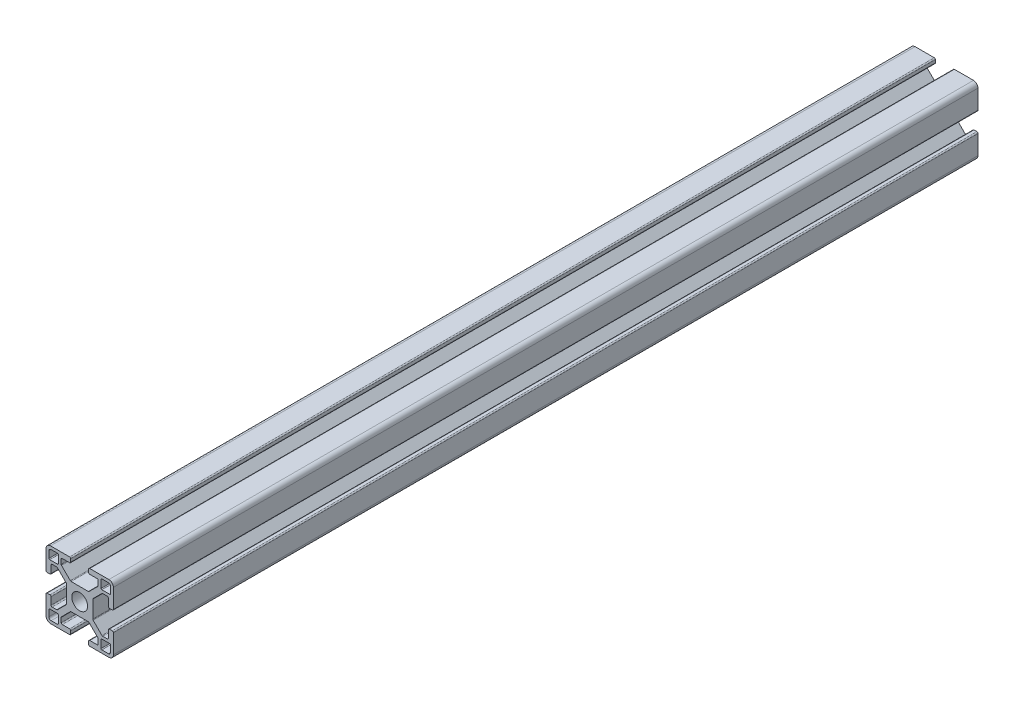
SolidWorks part; units mm, degrees
ref_plane "Front Plane" through (0, 0, 0) normal (0, 0, 1) x (1, 0, 0)
ref_plane "Top Plane" through (0, 0, 0) normal (0, 1, 0) x (1, 0, 0)
ref_plane "Right Plane" through (0, 0, 0) normal (1, 0, 0) x (0, 0, -1)
sketch "Sketch1" plane through (0, 0, 0) normal (0, 0, 1) x (1, 0, 0)
  line L0 (3.9799, -2.4733) -> (3.1981, -1.4942) construction
  line L1 (1.4942, -3.1981) -> (2.4733, -3.9799) construction
  line L2 (-2.4733, -3.9799) -> (-1.4942, -3.1981) construction
  line L3 (-3.1981, -1.4942) -> (-3.9799, -2.4733) construction
  line L4 (-3.9799, 2.4733) -> (-3.1981, 1.4942) construction
  line L5 (-1.4942, 3.1981) -> (-2.4733, 3.9799) construction
  line L6 (2.4733, 3.9799) -> (1.4942, 3.1981) construction
  line L7 (3.1981, 1.4942) -> (3.9799, 2.4733) construction
  line L8 (-12.6999, -13.6999) -> (-9.881, -13.6999)
  line L9 (-13.6999, -9.881) -> (-13.6999, -12.6999)
  line L10 (-9.88, -9.5) -> (-13.3189, -9.5)
  line L11 (-9.5, -13.3189) -> (-9.5, -9.88)
  line L12 (13.6999, -12.6999) -> (13.6999, -9.881)
  line L13 (9.881, -13.6999) -> (12.6999, -13.6999)
  line L14 (9.5, -9.88) -> (9.5, -13.3189)
  line L15 (13.3189, -9.5) -> (9.88, -9.5)
  line L16 (9.88, 9.5) -> (13.3189, 9.5)
  line L17 (9.5, 13.3189) -> (9.5, 9.88)
  line L18 (12.6999, 13.6999) -> (9.881, 13.6999)
  line L19 (13.6999, 9.881) -> (13.6999, 12.6999)
  line L20 (-13.6999, 12.6999) -> (-13.6999, 9.881)
  line L21 (-9.881, 13.6999) -> (-12.6999, 13.6999)
  line L22 (-9.5, 9.88) -> (-9.5, 13.3189)
  line L23 (-13.3189, 9.5) -> (-9.88, 9.5)
  line L24 (14.4999, -4) -> (13.2425, -4)
  line L25 (12.7425, -4.5) -> (12.7425, -7.7325)
  line L26 (12.2428, -8.25) -> (10.2602, -8.25)
  line L27 (9.9066, -8.1035) -> (5.9811, -4.178)
  line L28 (5.8347, -3.8245) -> (5.8347, -1.0125)
  line L29 (5.8347, -1.0125) -> (5.3247, -0.0625) construction
  line L30 (5.3247, -0.0625) -> (5.8347, 0.8875) construction
  line L31 (5.8347, 0.8875) -> (5.8347, 3.8245)
  line L32 (5.9811, 4.178) -> (9.9066, 8.1035)
  line L33 (10.2602, 8.25) -> (12.2428, 8.25)
  line L34 (12.7425, 7.7325) -> (12.7425, 4.5)
  line L35 (13.2425, 4) -> (14.4999, 4)
  line L36 (14.9999, 4.5) -> (14.9999, 12.9999)
  line L37 (12.9999, 14.9999) -> (4.5, 14.9999)
  line L38 (4, 14.4999) -> (4, 13.2425)
  line L39 (4.5, 12.7425) -> (7.7325, 12.7425)
  line L40 (8.25, 12.2428) -> (8.25, 10.2602)
  line L41 (8.1035, 9.9066) -> (4.178, 5.9811)
  line L42 (3.8245, 5.8347) -> (0.95, 5.8347)
  line L43 (0.95, 5.8347) -> (0, 5.3247) construction
  line L44 (0, 5.3247) -> (-0.95, 5.8347) construction
  line L45 (-0.95, 5.8347) -> (-3.8245, 5.8347)
  line L46 (-4.178, 5.9811) -> (-8.1035, 9.9066)
  line L47 (-8.25, 10.2602) -> (-8.25, 12.2428)
  line L48 (-7.7325, 12.7425) -> (-4.5, 12.7425)
  line L49 (-4, 13.2425) -> (-4, 14.4999)
  line L50 (-4.5, 14.9999) -> (-12.9999, 14.9999)
  line L51 (-14.9999, 12.9999) -> (-14.9999, 4.5)
  line L52 (-14.4999, 4) -> (-13.2425, 4)
  line L53 (-12.7425, 4.5) -> (-12.7425, 7.7325)
  line L54 (-12.2428, 8.25) -> (-10.2602, 8.25)
  line L55 (-9.9066, 8.1035) -> (-5.9811, 4.178)
  line L56 (-5.8347, 3.8245) -> (-5.8347, 0.8875)
  line L57 (-5.8347, 0.8875) -> (-5.3247, -0.0625) construction
  line L58 (-5.3247, -0.0625) -> (-5.8347, -1.0125) construction
  line L59 (-5.8347, -1.0125) -> (-5.8347, -3.8245)
  line L60 (-5.9811, -4.178) -> (-9.9066, -8.1035)
  line L61 (-10.2602, -8.25) -> (-12.2428, -8.25)
  line L62 (-12.7425, -7.7325) -> (-12.7425, -4.5)
  line L63 (-13.2425, -4) -> (-14.4999, -4)
  line L64 (-14.9999, -4.5) -> (-14.9999, -12.9999)
  line L65 (-12.9999, -14.9999) -> (-4.5, -14.9999)
  line L66 (-4, -14.4999) -> (-4, -13.2425)
  line L67 (-4.5, -12.7425) -> (-7.7325, -12.7425)
  line L68 (-8.25, -12.2428) -> (-8.25, -10.2602)
  line L69 (-8.1035, -9.9066) -> (-4.178, -5.9811)
  line L70 (-3.8245, -5.8347) -> (-0.95, -5.8347)
  line L71 (-0.95, -5.8347) -> (0, -5.3247) construction
  line L72 (0, -5.3247) -> (0.95, -5.8347) construction
  line L73 (0.95, -5.8347) -> (3.8245, -5.8347)
  line L74 (4.178, -5.9811) -> (8.1035, -9.9066)
  line L75 (8.25, -10.2602) -> (8.25, -12.2428)
  line L76 (7.7325, -12.7425) -> (4.5, -12.7425)
  line L77 (4, -13.2425) -> (4, -14.4999)
  line L78 (4.5, -14.9999) -> (12.9999, -14.9999)
  line L79 (14.9999, -12.9999) -> (14.9999, -4.5)
  line L80 (-5.8347, -1.0125) -> (-5.8347, 0.8875)
  line L81 (-0.95, 5.8347) -> (0.95, 5.8347)
  line L82 (5.8347, 0.8875) -> (5.8347, -1.0125)
  line L83 (-0.95, -5.8347) -> (0.95, -5.8347)
  arc A0 (2.4733, -3.9799) -> (3.9799, -2.4733) centre (3.1422, -3.1422) ccw construction
  arc A1 (-1.4942, -3.1981) -> (1.4942, -3.1981) centre (0, 0) ccw construction
  arc A2 (-3.9799, -2.4733) -> (-2.4733, -3.9799) centre (-3.1422, -3.1422) ccw construction
  arc A3 (-3.1981, 1.4942) -> (-3.1981, -1.4942) centre (0, 0) ccw construction
  arc A4 (-2.4733, 3.9799) -> (-3.9799, 2.4733) centre (-3.1422, 3.1422) ccw construction
  arc A5 (1.4942, 3.1981) -> (-1.4942, 3.1981) centre (0, 0) ccw construction
  arc A6 (3.9799, 2.4733) -> (2.4733, 3.9799) centre (3.1422, 3.1422) ccw construction
  arc A7 (3.1981, -1.4942) -> (3.1981, 1.4942) centre (0, 0) ccw construction
  arc A8 (-13.6999, -12.6999) -> (-12.6999, -13.6999) centre (-12.6999, -12.6999) ccw
  arc A9 (-13.3189, -9.5) -> (-13.6999, -9.881) centre (-13.3189, -9.881) ccw
  arc A10 (-9.5, -9.88) -> (-9.88, -9.5) centre (-9.88, -9.88) ccw
  arc A11 (-9.881, -13.6999) -> (-9.5, -13.3189) centre (-9.881, -13.3189) ccw
  arc A12 (12.6999, -13.6999) -> (13.6999, -12.6999) centre (12.6999, -12.6999) ccw
  arc A13 (9.5, -13.3189) -> (9.881, -13.6999) centre (9.881, -13.3189) ccw
  arc A14 (9.88, -9.5) -> (9.5, -9.88) centre (9.88, -9.88) ccw
  arc A15 (13.6999, -9.881) -> (13.3189, -9.5) centre (13.3189, -9.881) ccw
  arc A16 (9.5, 9.88) -> (9.88, 9.5) centre (9.88, 9.88) ccw
  arc A17 (9.881, 13.6999) -> (9.5, 13.3189) centre (9.881, 13.3189) ccw
  arc A18 (13.6999, 12.6999) -> (12.6999, 13.6999) centre (12.6999, 12.6999) ccw
  arc A19 (13.3189, 9.5) -> (13.6999, 9.881) centre (13.3189, 9.881) ccw
  arc A20 (14.9999, -4.5) -> (14.4999, -4) centre (14.4999, -4.5) ccw
  arc A21 (13.2425, -4) -> (12.7425, -4.5) centre (13.2425, -4.5) ccw
  arc A22 (12.2428, -8.25) -> (12.7425, -7.7325) centre (12.2428, -7.75) ccw
  arc A23 (9.9066, -8.1035) -> (10.2602, -8.25) centre (10.2602, -7.75) ccw
  arc A24 (5.8347, -3.8245) -> (5.9811, -4.178) centre (6.3347, -3.8245) ccw
  arc A25 (5.9811, 4.178) -> (5.8347, 3.8245) centre (6.3347, 3.8245) ccw
  arc A26 (10.2602, 8.25) -> (9.9066, 8.1035) centre (10.2602, 7.75) ccw
  arc A27 (12.7425, 7.7325) -> (12.2428, 8.25) centre (12.2428, 7.75) ccw
  arc A28 (12.7425, 4.5) -> (13.2425, 4) centre (13.2425, 4.5) ccw
  arc A29 (14.4999, 4) -> (14.9999, 4.5) centre (14.4999, 4.5) ccw
  arc A30 (14.9999, 12.9999) -> (12.9999, 14.9999) centre (12.9999, 12.9999) ccw
  arc A31 (4.5, 14.9999) -> (4, 14.4999) centre (4.5, 14.4999) ccw
  arc A32 (4, 13.2425) -> (4.5, 12.7425) centre (4.5, 13.2425) ccw
  arc A33 (8.25, 12.2428) -> (7.7325, 12.7425) centre (7.75, 12.2428) ccw
  arc A34 (8.1035, 9.9066) -> (8.25, 10.2602) centre (7.75, 10.2602) ccw
  arc A35 (3.8245, 5.8347) -> (4.178, 5.9811) centre (3.8245, 6.3347) ccw
  arc A36 (-4.178, 5.9811) -> (-3.8245, 5.8347) centre (-3.8245, 6.3347) ccw
  arc A37 (-8.25, 10.2602) -> (-8.1035, 9.9066) centre (-7.75, 10.2602) ccw
  arc A38 (-7.7325, 12.7425) -> (-8.25, 12.2428) centre (-7.75, 12.2428) ccw
  arc A39 (-4.5, 12.7425) -> (-4, 13.2425) centre (-4.5, 13.2425) ccw
  arc A40 (-4, 14.4999) -> (-4.5, 14.9999) centre (-4.5, 14.4999) ccw
  arc A41 (-12.9999, 14.9999) -> (-14.9999, 12.9999) centre (-12.9999, 12.9999) ccw
  arc A42 (-14.9999, 4.5) -> (-14.4999, 4) centre (-14.4999, 4.5) ccw
  arc A43 (-13.2425, 4) -> (-12.7425, 4.5) centre (-13.2425, 4.5) ccw
  arc A44 (-12.2428, 8.25) -> (-12.7425, 7.7325) centre (-12.2428, 7.75) ccw
  arc A45 (-9.9066, 8.1035) -> (-10.2602, 8.25) centre (-10.2602, 7.75) ccw
  arc A46 (-5.8347, 3.8245) -> (-5.9811, 4.178) centre (-6.3347, 3.8245) ccw
  arc A47 (-5.9811, -4.178) -> (-5.8347, -3.8245) centre (-6.3347, -3.8245) ccw
  arc A48 (-10.2602, -8.25) -> (-9.9066, -8.1035) centre (-10.2602, -7.75) ccw
  arc A49 (-12.7425, -7.7325) -> (-12.2428, -8.25) centre (-12.2428, -7.75) ccw
  arc A50 (-12.7425, -4.5) -> (-13.2425, -4) centre (-13.2425, -4.5) ccw
  arc A51 (-14.4999, -4) -> (-14.9999, -4.5) centre (-14.4999, -4.5) ccw
  arc A52 (-14.9999, -12.9999) -> (-12.9999, -14.9999) centre (-12.9999, -12.9999) ccw
  arc A53 (-4.5, -14.9999) -> (-4, -14.4999) centre (-4.5, -14.4999) ccw
  arc A54 (-4, -13.2425) -> (-4.5, -12.7425) centre (-4.5, -13.2425) ccw
  arc A55 (-8.25, -12.2428) -> (-7.7325, -12.7425) centre (-7.75, -12.2428) ccw
  arc A56 (-8.1035, -9.9066) -> (-8.25, -10.2602) centre (-7.75, -10.2602) ccw
  arc A57 (-3.8245, -5.8347) -> (-4.178, -5.9811) centre (-3.8245, -6.3347) ccw
  arc A58 (4.178, -5.9811) -> (3.8245, -5.8347) centre (3.8245, -6.3347) ccw
  arc A59 (8.25, -10.2602) -> (8.1035, -9.9066) centre (7.75, -10.2602) ccw
  arc A60 (7.7325, -12.7425) -> (8.25, -12.2428) centre (7.75, -12.2428) ccw
  arc A61 (4.5, -12.7425) -> (4, -13.2425) centre (4.5, -13.2425) ccw
  arc A62 (4, -14.4999) -> (4.5, -14.9999) centre (4.5, -14.4999) ccw
  arc A63 (12.9999, -14.9999) -> (14.9999, -12.9999) centre (12.9999, -12.9999) ccw
  arc A64 (-12.6999, 13.6999) -> (-13.6999, 12.6999) centre (-12.6999, 12.6999) ccw
  arc A65 (-9.5, 13.3189) -> (-9.881, 13.6999) centre (-9.881, 13.3189) ccw
  arc A66 (-9.88, 9.5) -> (-9.5, 9.88) centre (-9.88, 9.88) ccw
  arc A67 (-13.6999, 9.881) -> (-13.3189, 9.5) centre (-13.3189, 9.881) ccw
  circle A68 centre (0, 0) radius 3.53
extrude "Boss-Extrude1" add sketch "Sketch1" along normal mid plane 385
